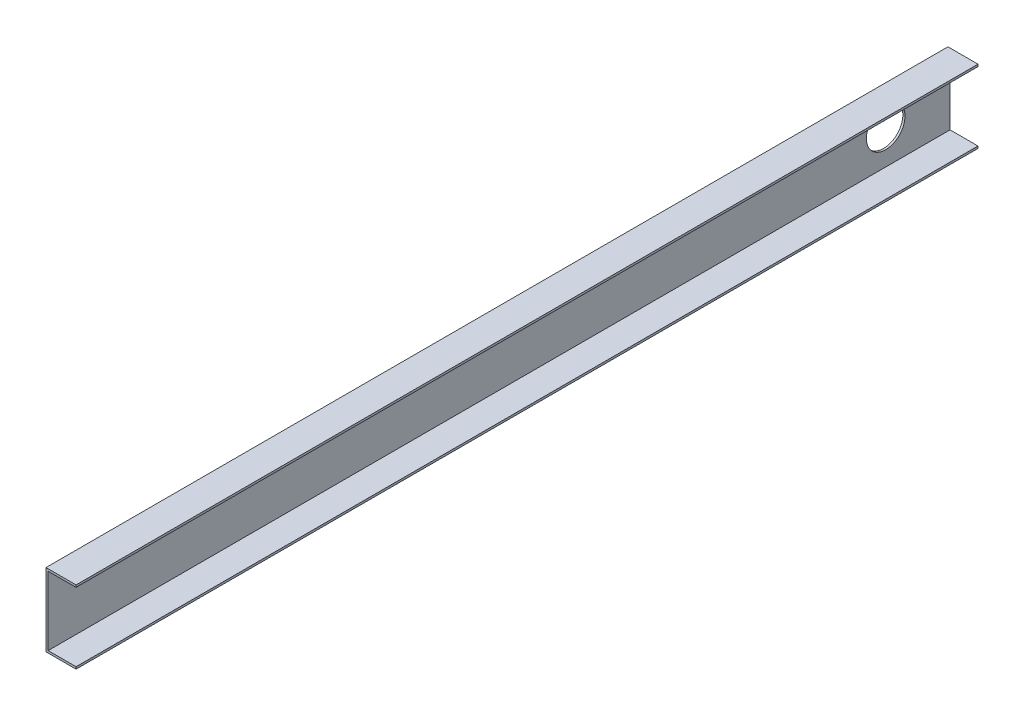
SolidWorks part; units mm, degrees
material "1.4000 (X6Cr13)"
ref_plane "Plano frontal" through (0, 0, 0) normal (0, 0, 1) x (1, 0, 0)
ref_plane "Plano superior" through (0, 0, 0) normal (0, 1, 0) x (1, 0, 0)
ref_plane "Plano direito" through (0, 0, 0) normal (1, 0, 0) x (0, 0, -1)
sketch "Esboço1" plane through (0, 0, 0) normal (0, 0, 1) x (1, 0, 0)
  line L0 (0, -8.5) -> (0, 8.5)
  line L1 (0, 8.5) -> (7, 8.5)
  line L2 (0, -8.5) -> (7, -8.5)
  line L3 (0.5, -8) -> (7, -8)
  line L4 (0.5, -8) -> (0.5, 8)
  line L5 (0.5, 8) -> (7, 8)
  line L6 (7, -8.5) -> (7, -8)
  line L7 (7, 8.5) -> (7, 8)
  point P4 (0, 0)
  dimension "D1" = 17
  dimension "D2" = 7
  dimension "D3" = 0.5
extrude "Ressalto-extrusão1" add sketch "Esboço1" along normal blind 210
sketch "Esboço3" plane through (0, 0, 0) normal (-1, 0, 0) x (0, 0, 1)
  circle A0 centre (15, 0) radius 4.5
  dimension "D1" = 9
  dimension "D2" = 15
extrude "Corte-extrusão1" cut sketch "Esboço3" against normal blind 10
